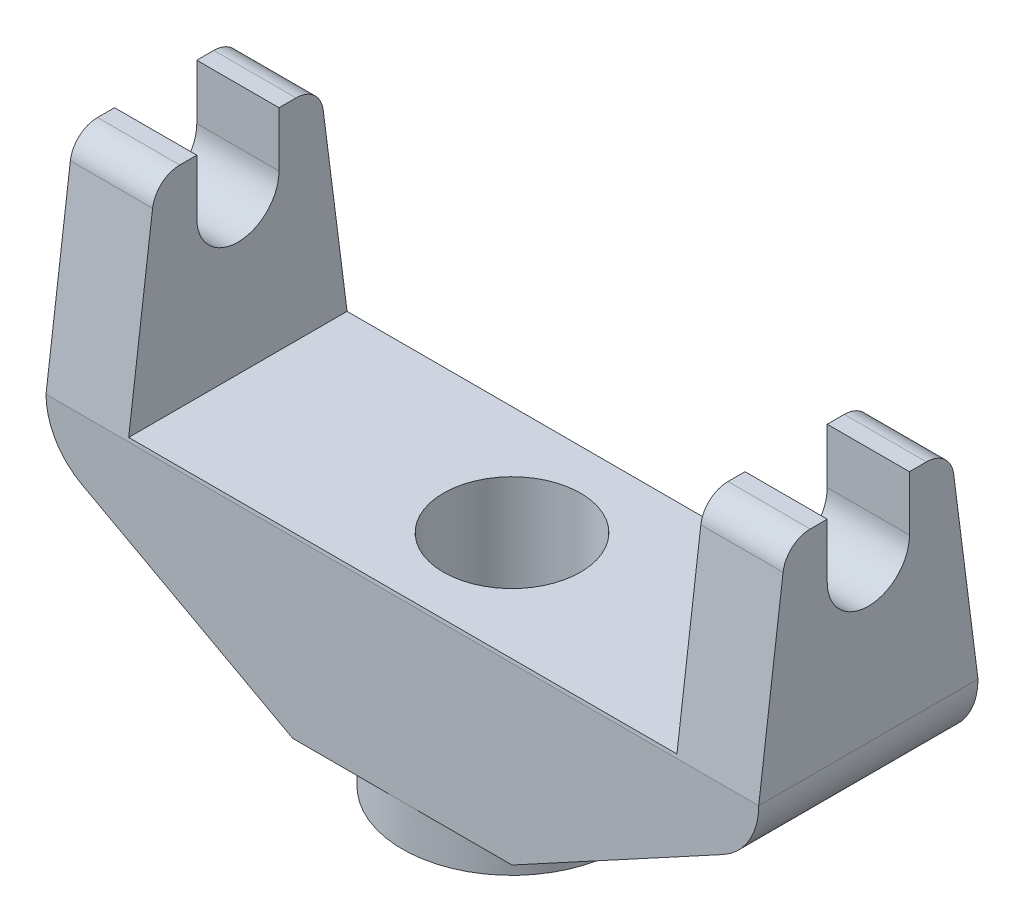
SolidWorks part; units mm, degrees
ref_plane "Front Plane" through (0, 0, 0) normal (0, 0, 1) x (1, 0, 0)
ref_plane "Top Plane" through (0, 0, 0) normal (0, 1, 0) x (1, 0, 0)
ref_plane "Right Plane" through (0, 0, 0) normal (1, 0, 0) x (0, 0, -1)
sketch "Sketch1" plane through (0, 0, 0) normal (0, 0, 1) x (1, 0, 0)
  line L0 (0, 0) -> (0, 82.55) construction
  line L1 (-50.8, 0) -> (50.8, 0)
  line L2 (-127, 82.55) -> (127, 82.55)
  line L3 (127, 82.55) -> (127, 180.0368)
  line L4 (127, 180.0368) -> (165.1, 180.0368)
  line L5 (165.1, 180.0368) -> (165.1, 80.9403)
  line L6 (50.8, 0) -> (148.4979, 53.0368)
  line L7 (-50.8, 0) -> (-148.4979, 53.0368)
  line L8 (-165.1, 180.0368) -> (-165.1, 80.9403)
  line L9 (-127, 180.0368) -> (-165.1, 180.0368)
  line L10 (-127, 82.55) -> (-127, 180.0368)
  arc A0 (-148.4979, 53.0368) -> (-165.1, 80.9403) centre (-133.35, 80.9403) cw
  arc A1 (148.4979, 53.0368) -> (165.1, 80.9403) centre (133.35, 80.9403) ccw
  point P10 (148.4979, 53.0368)
  dimension "D7" = 31.75
  dimension "D1" = 82.55
  dimension "D2" = 50.8
  dimension "D3" = 127
  dimension "D4" = 38.1
  dimension "D5" = 127
  dimension "D6" = 148.4979
extrude "Boss-Extrude1" add sketch "Sketch1" along normal mid plane 101.6
sketch "Sketch2" plane through (0, 0, 0) normal (0, -1, 0) x (1, 0, 0)
  circle A0 centre (0, 0) radius 50.8
  dimension "D1" = 101.6
extrude "Boss-Extrude2" add sketch "Sketch2" along normal blind 19.05 and the other way up to surface
sketch "Sketch3" plane through (0, 82.55, 0) normal (0, 1, 0) x (1, 0, 0)
  circle A0 centre (0, 0) radius 31.75
  dimension "D1" = 63.5
extrude "Cut-Extrude1" cut sketch "Sketch3" against normal through all
sketch "Sketch4" plane through (165.1, 0, 0) normal (1, 0, 0) x (0, 0, -1)
  line L0 (-50.8, 180.0368) -> (50.8, 180.0368) construction
  line L1 (-50.8, 80.9403) -> (-38.1, 180.0368)
  line L2 (-38.1, 180.0368) -> (-19.05, 180.0368)
  line L3 (38.1, 180.0368) -> (50.8, 80.9403)
  line L4 (-19.05, 154.6368) -> (-19.05, 180.0368)
  line L5 (19.05, 154.6368) -> (19.05, 180.0368)
  line L6 (19.05, 180.0368) -> (38.1, 180.0368)
  line L8 (-50.8, 80.9403) -> (50.8, 80.9403)
  line L9 (-50.8, 80.9403) -> (-50.8, 180.0368)
  line L10 (-50.8, 180.0368) -> (50.8, 180.0368)
  line L11 (50.8, 80.9403) -> (50.8, 180.0368)
  arc A0 (-19.05, 154.6368) -> (19.05, 154.6368) centre (0, 154.6368) ccw
  point P7 (0, 180.0368)
  point P11 (0, 180.0368)
  line M8 (50.8, 80.9403) -> (50.8, 180.0368)
  line M9 (50.8, 180.0368) -> (-50.8, 180.0368)
  line M10 (-50.8, 180.0368) -> (-50.8, 80.9403)
  dimension "D1" = 38.1
  dimension "D2" = 25.4
  dimension "D3" = 76.2
  dimension "D4" = 19.05
  dimension "D5" = 38.1
extrude "Cut-Extrude2" cut sketch "Sketch4" against normal through all contours L1 M10 M9 | L4 A0 L5 M9 | L3 M9 M8
fillet "Fillet1" radius 12.7 4 edges at (146.05, 180.0368, -38.1) (-146.05, 180.0368, -38.1) (-146.05, 180.0368, 38.1) (146.05, 180.0368, 38.1)
